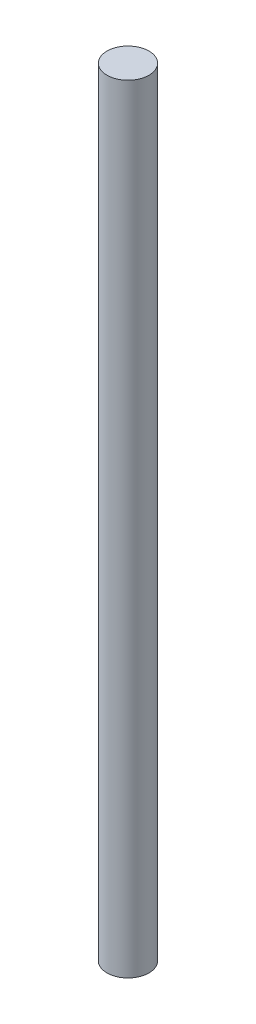
SolidWorks part; units mm, degrees
ref_plane "Alzado" through (0, 0, 0) normal (0, 0, 1) x (1, 0, 0)
ref_plane "Planta" through (0, 0, 0) normal (0, 1, 0) x (1, 0, 0)
ref_plane "Vista lateral" through (0, 0, 0) normal (1, 0, 0) x (0, 0, -1)
sketch "Croquis1" plane through (0, 0, 0) normal (0, 1, 0) x (1, 0, 0)
  circle A0 centre (0, 0) radius 4
  dimension "D1" = 8
extrude "Saliente-Extruir1" add sketch "Croquis1" along normal blind 148.26
